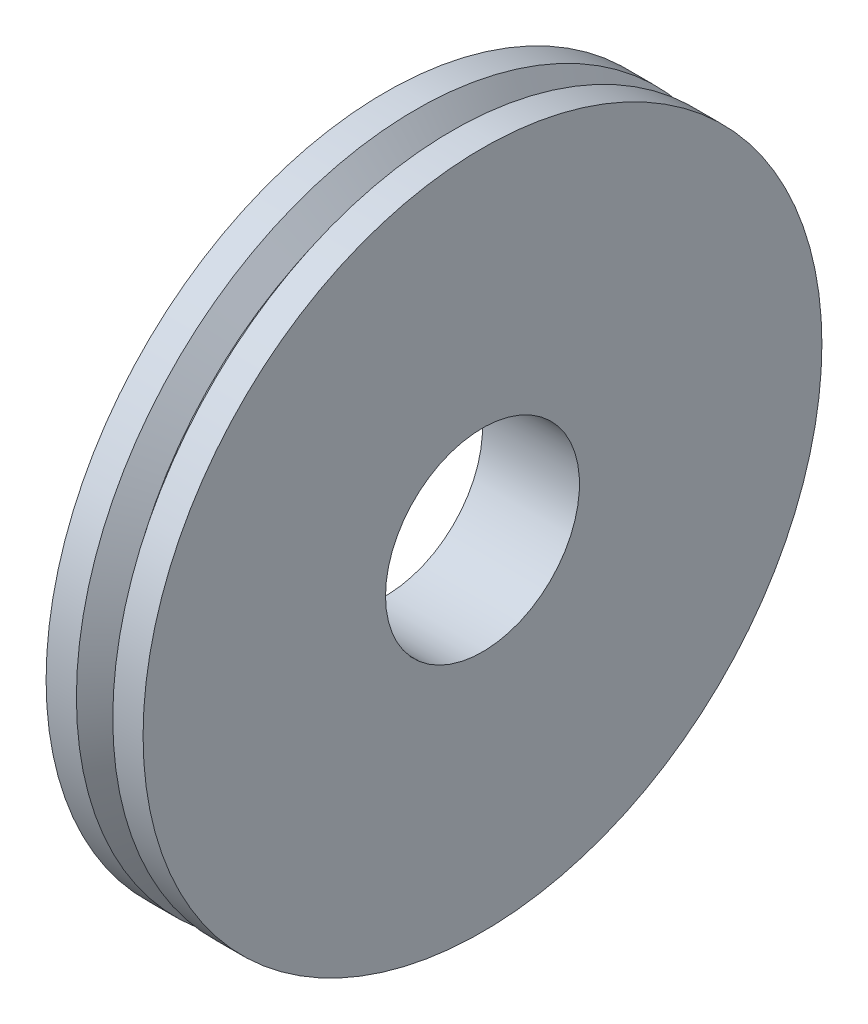
SolidWorks part; units mm, degrees
material "ABS"
ref_plane "前视基准面" through (0, 0, 0) normal (0, 0, 1) x (1, 0, 0)
ref_plane "上视基准面" through (0, 0, 0) normal (0, 1, 0) x (1, 0, 0)
ref_plane "右视基准面" through (0, 0, 0) normal (1, 0, 0) x (0, 0, -1)
sketch "草图1" plane through (0, 0, 0) normal (0, 0, 1) x (1, 0, 0)
  line L0 (-33.4645, 0) -> (35.5797, 0) construction
  line L1 (-5.0655, 4) -> (-5.0655, 14)
  line L2 (-3.8155, 14) -> (-3.0655, 13)
  line L3 (-3.0655, 13) -> (-2.3155, 14)
  line L4 (-2.3155, 14) -> (-1.0655, 14)
  line L5 (-1.0655, 14) -> (-1.0655, 4)
  line L6 (-1.0655, 4) -> (-5.0655, 4)
  line L7 (-3.8155, 14) -> (-5.0655, 14)
  dimension "D1" = 8
  dimension "D2" = 1.25
  dimension "D3" = 1.25
  dimension "D4" = 1.5
  dimension "D5" = 1
  dimension "D6" = 0.75
  dimension "D7" = 28
revolve "旋转1" add sketch "草图1" angle 360 about L0
